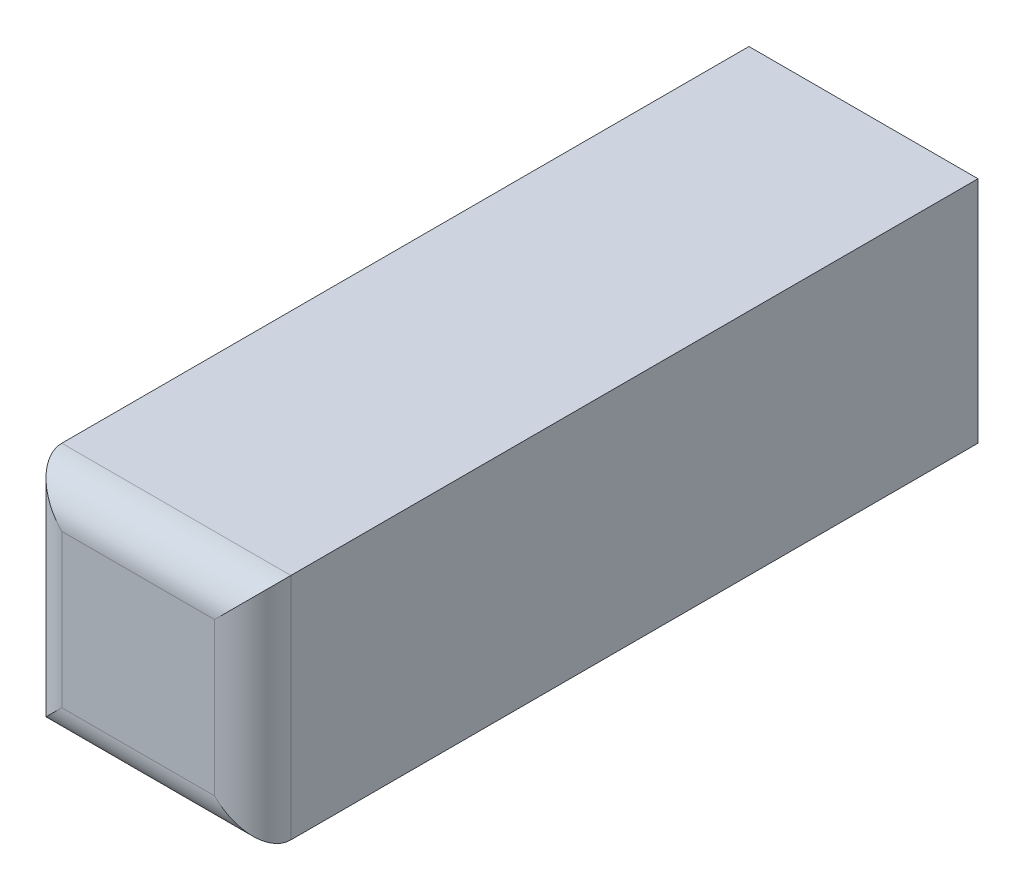
SolidWorks part; units mm, degrees
ref_plane "Płaszczyzna przednia" through (0, 0, 0) normal (0, 0, 1) x (1, 0, 0)
ref_plane "Płaszczyzna górna" through (0, 0, 0) normal (0, 1, 0) x (1, 0, 0)
ref_plane "Płaszczyzna prawa" through (0, 0, 0) normal (1, 0, 0) x (0, 0, -1)
sketch "Sketch1" plane through (0, 0, 0) normal (0, 0, 1) x (1, 0, 0)
  line L1 (3, -3) -> (-3, -3)
  line L2 (3, -3) -> (3, 3)
  line L3 (3, 3) -> (-3, 3)
  line L4 (-3, -3) -> (-3, 3)
  line L5 (3, -3) -> (-3, 3) construction
  line L6 (3, 3) -> (-3, -3) construction
  point P0 (0, 0)
  point P5 (0, 0)
  point P6 (0, 0)
  dimension "D1" = 6
  dimension "D2" = 6
  dimension "D3" = 90
extrude "Boss-Extrude1" add sketch "Sketch1" along normal blind 19
sketch "Sketch2" plane through (0, 0, 0) normal (0, 0, -1) x (-1, 0, 0)
  circle A0 centre (0, 0) radius 1.8
  dimension "D1" = 3.6
extrude "Cut-Extrude1" cut sketch "Sketch2" against normal blind 5
fillet "Fillet1" radius 1 4 edges at (0, -3, 19) (-3, 0, 19) (0, 3, 19) (3, 0, 19)
